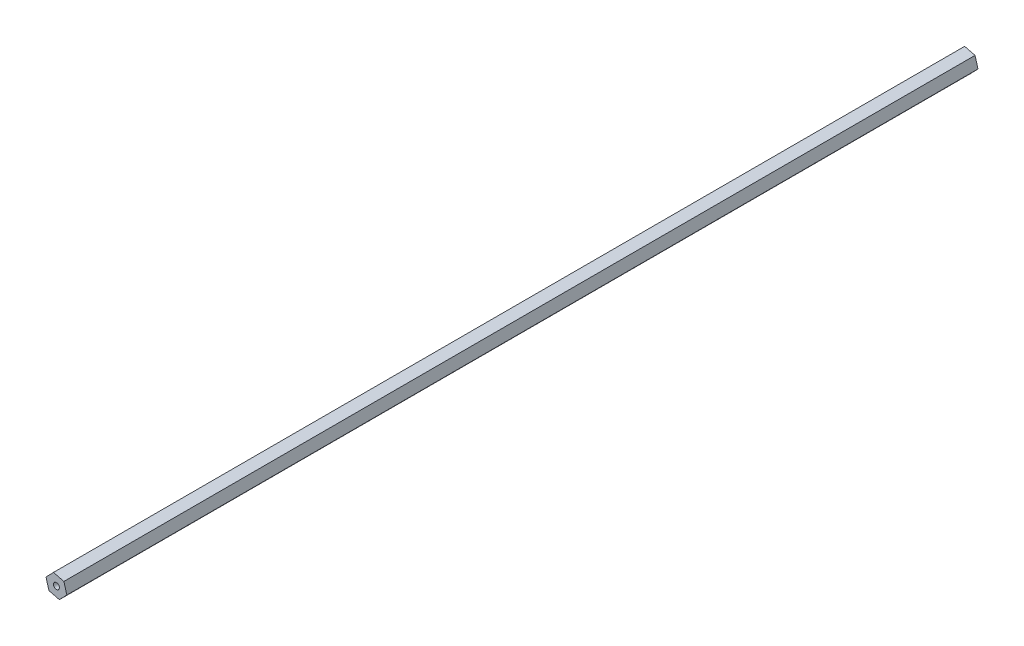
SolidWorks part; units mm, degrees
ref_plane "Front Plane" through (0, 0, 0) normal (0, 0, 1) x (1, 0, 0)
ref_plane "Top Plane" through (0, 0, 0) normal (0, 1, 0) x (1, 0, 0)
ref_plane "Right Plane" through (0, 0, 0) normal (1, 0, 0) x (0, 0, -1)
sketch "Sketch1" plane through (0, 0, 0) normal (0, 0, 1) x (1, 0, 0)
  line L1 (-7.1134, 1.7784) -> (-5.0968, -5.2712)
  line L2 (-5.0968, -5.2712) -> (2.0166, -7.0496)
  line L3 (2.0166, -7.0496) -> (7.1134, -1.7784)
  line L4 (7.1134, -1.7784) -> (5.0968, 5.2712)
  line L5 (5.0968, 5.2712) -> (-2.0166, 7.0496)
  line L6 (-2.0166, 7.0496) -> (-7.1134, 1.7784)
  circle A0 centre (0, 0) radius 6.35 construction
  dimension "D1" = 12.7
extrude "Boss-Extrude1" add sketch "Sketch1" along normal blind 622.046
sketch "Sketch2" plane through (0, 0, 622.046) normal (0, 0, 1) x (1, 0, 0)
  circle A0 centre (0, 0) radius 2.032
  dimension "D1" = 4.064
extrude "Cut-Extrude1" cut sketch "Sketch2" against normal blind 736.6
